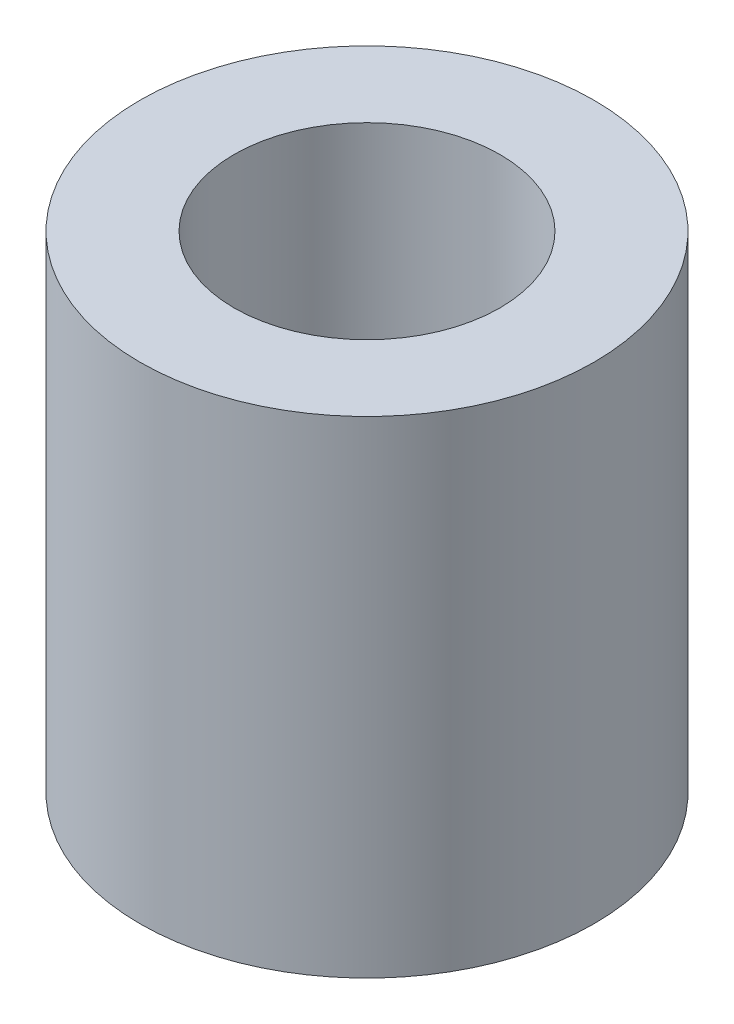
SolidWorks part; units mm, degrees
ref_plane "Спереди" through (0, 0, 0) normal (0, 0, 1) x (1, 0, 0)
ref_plane "Сверху" through (0, 0, 0) normal (0, 1, 0) x (1, 0, 0)
ref_plane "Справа" through (0, 0, 0) normal (1, 0, 0) x (0, 0, -1)
sketch "Sketch1" plane through (0, 0, 0) normal (0, 1, 0) x (1, 0, 0)
  circle A0 centre (0, 0) radius 7
  dimension "D1" = 14
extrude "Boss-Extrude3" add sketch "Sketch1" along normal blind 15
sketch "Sketch4" plane through (0, 15, 0) normal (0, 1, 0) x (1, 0, 0)
  circle A0 centre (0, 0) radius 4.1
  dimension "D1" = 8.2
extrude "Cut-Extrude1" cut sketch "Sketch4" against normal through all
sketch "Sketch5" plane through (0, 0, 0) normal (0, -1, 0) x (1, 0, 0)
  circle A0 centre (0, 0) radius 6.1
  dimension "D1" = 12.2
extrude "Cut-Extrude2" cut sketch "Sketch5" against normal blind 3
